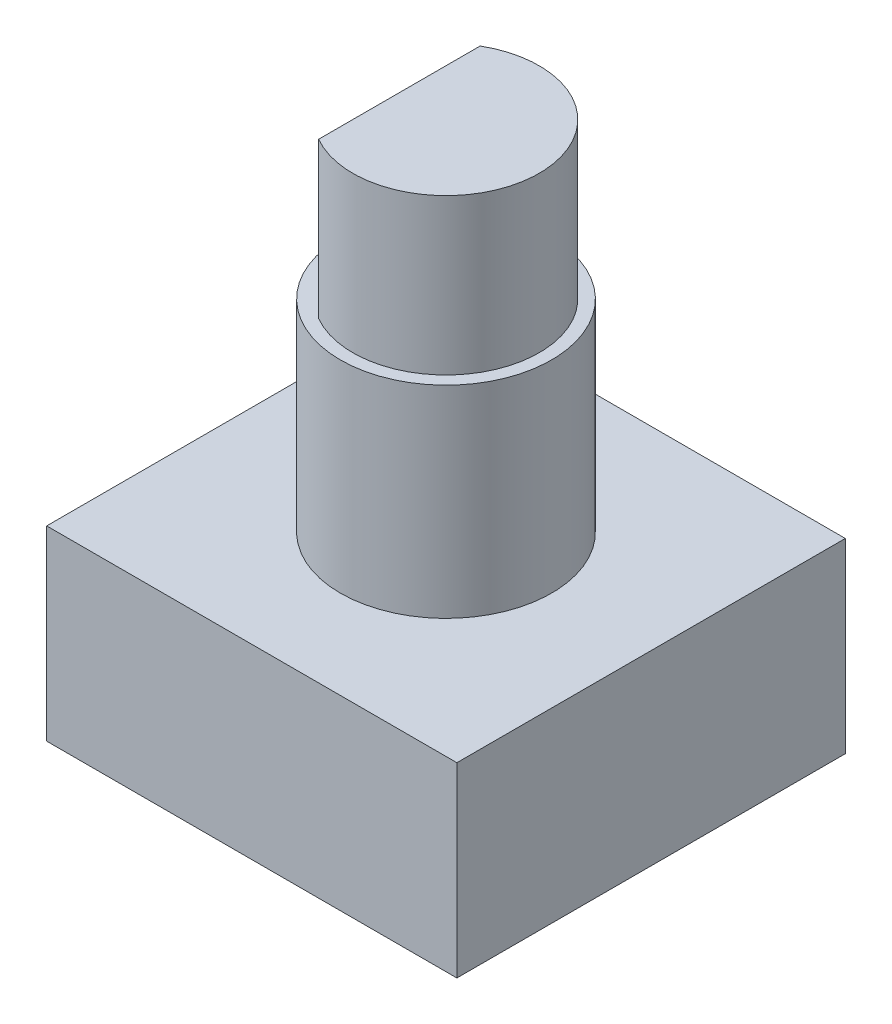
SolidWorks part; units mm, degrees
ref_plane "Front Plane" through (0, 0, 0) normal (0, 0, 1) x (1, 0, 0)
ref_plane "Top Plane" through (0, 0, 0) normal (0, 1, 0) x (1, 0, 0)
ref_plane "Right Plane" through (0, 0, 0) normal (1, 0, 0) x (0, 0, -1)
sketch "Sketch1" plane through (0, 0, 0) normal (0, 1, 0) x (1, 0, 0)
  line L1 (-6.6, 6.25) -> (6.6, 6.25)
  line L2 (-6.6, 6.25) -> (-6.6, -6.25)
  line L3 (-6.6, -6.25) -> (6.6, -6.25)
  line L4 (6.6, 6.25) -> (6.6, -6.25)
  line L5 (-6.6, 6.25) -> (6.6, -6.25) construction
  line L6 (-6.6, -6.25) -> (6.6, 6.25) construction
  point P0 (0, 0)
  dimension "D1" = 13.2
  dimension "D2" = 12.5
extrude "Boss-Extrude1" add sketch "Sketch1" along normal blind 6
sketch "Sketch2" plane through (0, 6, 0) normal (0, 1, 0) x (1, 0, 0)
  circle A0 centre (0, 0) radius 3.4
  dimension "D1" = 6.8
extrude "Boss-Extrude2" add sketch "Sketch2" along normal blind 6.5
sketch "Sketch3" plane through (0, 12.5, 0) normal (0, 1, 0) x (1, 0, 0)
  line L0 (-1.5, -2.5981) -> (-1.5, 2.5981)
  arc A0 (-1.5, -2.5981) -> (-1.5, 2.5981) centre (0, 0) ccw
  dimension "D1" = 6
  dimension "D2" = 1.5
extrude "Boss-Extrude3" add sketch "Sketch3" along normal blind 5
